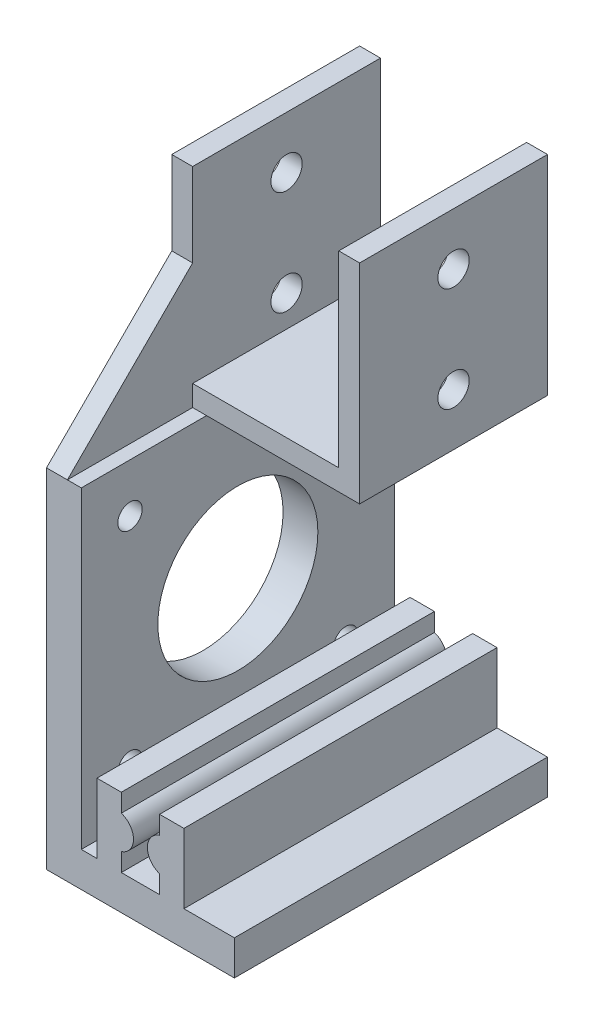
SolidWorks part; units mm, degrees
ref_plane "Front Plane" through (0, 0, 0) normal (0, 0, 1) x (1, 0, 0)
ref_plane "Top Plane" through (0, 0, 0) normal (0, 1, 0) x (1, 0, 0)
ref_plane "Right Plane" through (0, 0, 0) normal (1, 0, 0) x (0, 0, -1)
sketch "Sketch1" plane through (0, 0, 0) normal (0, 1, 0) x (1, 0, 0)
  line L1 (-13.5, 13.5) -> (13.5, 13.5)
  line L2 (-13.5, 13.5) -> (-13.5, -13.5)
  line L3 (-13.5, -13.5) -> (13.5, -13.5)
  line L4 (13.5, 13.5) -> (13.5, -13.5)
  line L5 (-13.5, 13.5) -> (13.5, -13.5) construction
  line L6 (-13.5, -13.5) -> (13.5, 13.5) construction
  point P0 (0, 0)
  dimension "D1" = 27
  dimension "D2" = 27
extrude "Boss-Extrude1" add sketch "Sketch1" along normal blind 30
sketch "Sketch2" plane through (0, 0, -13.5) normal (0, 0, -1) x (-1, 0, 0)
  line L0 (-10.5, 30) -> (-10.5, 3)
  line L1 (-13.5, 30) -> (13.5, 30) construction
  line L2 (-10.5, 3) -> (10.5, 3)
  line L3 (10.5, 3) -> (10.5, 30)
  line L4 (10.5, 30) -> (-10.5, 30)
  line L5 (-13.5, 30) -> (-13.5, 0) construction
  line L6 (13.5, 30) -> (13.5, 0) construction
  line L7 (-13.5, 0) -> (13.5, 0) construction
  dimension "D1" = 3
  dimension "D2" = 3
  dimension "D3" = 3
extrude "Cut-Extrude1" cut sketch "Sketch2" against normal blind 30 contours L4 L0 L2 L3
sketch "Sketch3" plane through (-13.5, 0, 0) normal (-1, 0, 0) x (0, 0, 1)
  line L1 (-13.5, 30) -> (13.5, 30) construction
  line L2 (-13.5, 0) -> (13.5, 0) construction
  circle A0 centre (0, 7.5) radius 2.25
  circle A1 centre (0, 22.5) radius 2.25
  dimension "D1" = 4.5
  dimension "D2" = 4.5
  dimension "D3" = 7.5
  dimension "D4" = 7.5
extrude "Cut-Extrude2" cut sketch "Sketch3" against normal blind 30
sketch "Sketch5" plane through (0, 0, 0) normal (0, -1, 0) x (1, 0, 0)
  line L1 (-13.5, -13.5) -> (-8.5, -13.5)
  line L2 (-13.5, -13.5) -> (-13.5, 31.5)
  line L3 (-13.5, 31.5) -> (-8.5, 31.5)
  line L4 (-8.5, -13.5) -> (-8.5, 31.5)
  dimension "D1" = 45
  dimension "D2" = 5
extrude "Boss-Extrude2" add sketch "Sketch5" along normal blind 45
sketch "Sketch6" plane through (-8.5, 0, 0) normal (1, 0, 0) x (0, 0, -1)
  line L0 (13.5, -45) -> (-31.5, -45) construction
  line L1 (-31.5, -45) -> (-31.5, 0) construction
  line L2 (-13.5, 0) -> (-31.5, 0) construction
  line L3 (13.5, -45) -> (13.5, 0) construction
  line L4 (-13.5, 0) -> (13.5, 0) construction
  circle A0 centre (-24.5, -38) radius 1.75
  circle A1 centre (-24.5, -7) radius 1.75
  circle A2 centre (6.5, -7) radius 1.75
  circle A3 centre (6.5, -38) radius 1.75
  circle A4 centre (-9, -22.5) radius 11.5
  dimension "D1" = 3.5
  dimension "D2" = 3.5
  dimension "D3" = 3.5
  dimension "D4" = 3.5
  dimension "D5" = 7
  dimension "D6" = 7
  dimension "D7" = 7
  dimension "D8" = 7
  dimension "D9" = 7
  dimension "D10" = 7
  dimension "D11" = 7
  dimension "D12" = 7
  dimension "D13" = 23
  dimension "D14" = 22.5
  dimension "D15" = 22.5
  dimension "D16" = 31
extrude "Cut-Extrude3" cut sketch "Sketch6" against normal blind 10
sketch "Sketch8" plane through (-8.5, 0, 0) normal (1, 0, 0) x (0, 0, -1)
  line L1 (13.5, -45) -> (-31.5, -45)
  line L2 (13.5, -45) -> (13.5, -50)
  line L3 (13.5, -50) -> (-31.5, -50)
  line L4 (-31.5, -45) -> (-31.5, -50)
  dimension "D1" = 45
  dimension "D2" = 5
extrude "Boss-Extrude4" add sketch "Sketch8" against normal blind 5
sketch "Sketch9" plane through (-8.5, 0, 0) normal (1, 0, 0) x (0, 0, -1)
  line L0 (-31.5, -50) -> (-31.5, 0) construction
  line L1 (13.5, -50) -> (-31.5, -50)
  line L2 (13.5, -50) -> (13.5, -45)
  line L3 (13.5, -45) -> (-31.5, -45)
  line L4 (-31.5, -50) -> (-31.5, -45)
  dimension "D1" = 5
extrude "Boss-Extrude5" add sketch "Sketch9" along normal blind 22
sketch "Sketch10" plane through (0, 0, 31.5) normal (0, 0, 1) x (1, 0, 0)
  line L0 (13.5, -45) -> (-8.5, -45) construction
  line L1 (-6.25, -45) -> (-2.75, -45)
  line L2 (-6.25, -45) -> (-6.25, -35)
  line L3 (-6.25, -35) -> (-2.75, -35)
  line L4 (-2.75, -45) -> (-2.75, -35)
  line L6 (0, -45) -> (0, -35)
  line L7 (6.25, -35) -> (2.75, -35)
  line L8 (2.75, -45) -> (2.75, -35)
  line L9 (6.25, -45) -> (2.75, -45)
  line L10 (6.25, -45) -> (6.25, -35)
  circle A0 centre (-3.5, -40) radius 2.5
  circle A1 centre (3.5, -40) radius 2.5
  line M9 (13.5, -45) -> (-8.5, -45)
  dimension "D5" = 5
  dimension "D1" = 2.25
  dimension "D2" = 3.5
  dimension "D3" = 10
  dimension "D6" = 2.75
  dimension "D7" = 5.5
extrude "Boss-Extrude6" add sketch "Sketch10" against normal blind 45 contours A0 L4 L3 L2 M9 | L4 A0 | L4 A0 | A1 L8 | A1 L8 | L8 A1 L10 L7 M9
sketch "Sketch11" plane through (0, 0, 13.5) normal (0, 0, 1) x (1, 0, 0)
  line L1 (-13.5, 0) -> (-13.5, 12)
  line L2 (-13.5, 30) -> (-13.5, 0) construction
  line L3 (-13.5, 12) -> (-10.5, 12)
  line L4 (-10.5, 3) -> (-10.5, 30) construction
  line L5 (-10.5, 12) -> (-10.5, 3)
  dimension "D1" = 12
ref_plane "Plane5" through (-13.5, 0, 0) normal (-1, 0, 0) x (0, 0, 1)
sketch "Sketch15" plane through (-13.5, 0, 0) normal (-1, 0, 0) x (0, 0, 1)
  line L0 (31.5, 0) -> (13.5, 18)
  line L1 (13.5, 30) -> (13.5, 0) construction
  line L2 (13.5, 18) -> (13.5, 0)
  line L3 (13.5, 0) -> (31.5, 0)
  dimension "D1" = 18
  dimension "D2" = 18
extrude "Boss-Extrude10" add sketch "Sketch15" along normal up to surface (3 mm away) from surface at -3 up to face at (-13.5, -22.5, -2.5) starting at face at (-10.5, 7.5, 2.25)
sketch "Sketch16" plane through (0, 0, 13.5) normal (0, 0, 1) x (1, 0, 0)
  line L0 (-10.5, 3) -> (-8.5, 0)
  line L1 (-8.5, 0) -> (-10.5, 0)
  line L2 (-10.5, 0) -> (-10.5, 3)
